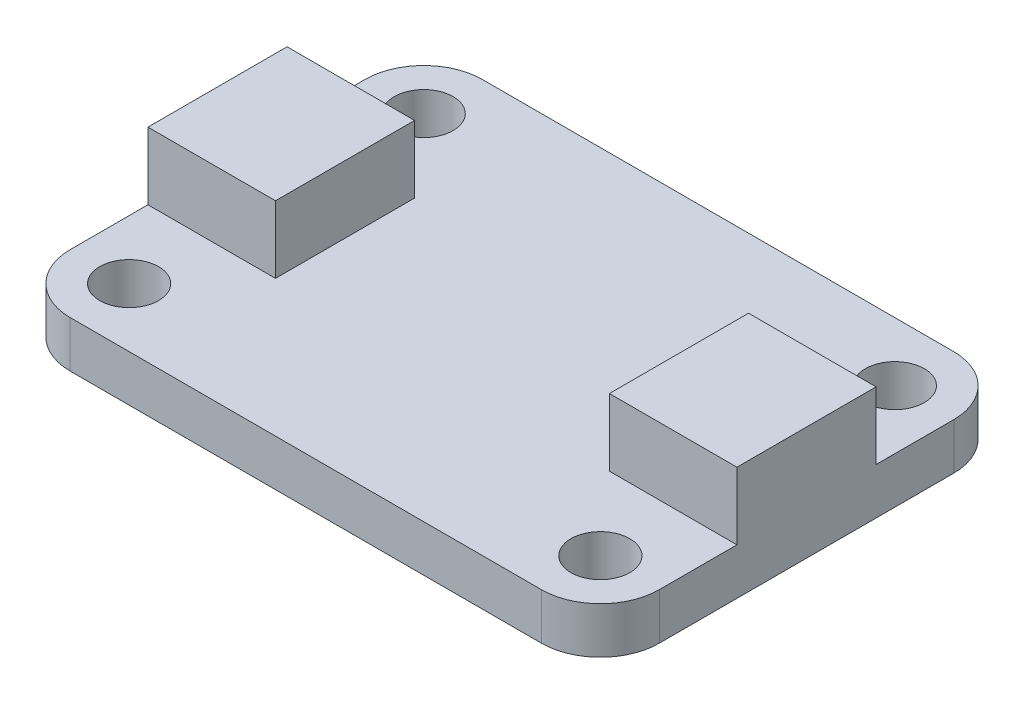
SolidWorks part; units mm, degrees
ref_plane "Front Plane" through (0, 0, 0) normal (0, 0, 1) x (1, 0, 0)
ref_plane "Top Plane" through (0, 0, 0) normal (0, 1, 0) x (1, 0, 0)
ref_plane "Right Plane" through (0, 0, 0) normal (1, 0, 0) x (0, 0, -1)
sketch "Sketch1" plane through (0, 0, 0) normal (0, 1, 0) x (1, 0, 0)
  line L1 (0, 0) -> (25.4, 0)
  line L2 (0, 0) -> (0, 17.78)
  line L3 (0, 17.78) -> (25.4, 17.78)
  line L4 (25.4, 0) -> (25.4, 17.78)
  dimension "D1" = 25.4
  dimension "D2" = 17.78
extrude "Boss-Extrude1" add sketch "Sketch1" along normal blind 2
sketch "Sketch2" plane through (0, 2, 0) normal (0, 1, 0) x (1, 0, 0)
  line L0 (0, 8.89) -> (25.4, 8.89) construction
  line L1 (0, 17.78) -> (0, 0) construction
  line L2 (25.4, 0) -> (25.4, 17.78) construction
  line L3 (12.7, 17.78) -> (12.7, 0) construction
  line L4 (25.4, 17.78) -> (0, 17.78) construction
  line L5 (0, 0) -> (25.4, 0) construction
  circle A0 centre (2.54, 15.24) radius 1.27
  circle A1 centre (22.86, 15.24) radius 1.27
  circle A2 centre (22.86, 2.54) radius 1.27
  circle A3 centre (2.54, 2.54) radius 1.27
  point P14 (0, 0)
  point P15 (22.86, 15.24)
  point P16 (1.2788, 17.148)
  point P21 (22.86, 2.54)
  dimension "D1" = 2.54
  dimension "D2" = 2.54
  dimension "D3" = 2.54
extrude "Cut-Extrude1" cut sketch "Sketch2" against normal through all
sketch "Sketch3" plane through (0, 2, 0) normal (0, 1, 0) x (1, 0, 0)
  line L0 (0, 8.89) -> (25.4, 8.89) construction
  line L1 (0, 17.78) -> (0, 0) construction
  line L2 (25.4, 0) -> (25.4, 17.78) construction
  line L3 (12.7, 17.78) -> (12.7, 0) construction
  line L4 (25.4, 17.78) -> (0, 17.78) construction
  line L5 (0, 0) -> (25.4, 0) construction
  line L6 (25.4, 5.89) -> (19.9, 5.89)
  line L7 (0, 11.89) -> (5.5, 11.89)
  line L8 (0, 11.89) -> (0, 5.89)
  line L9 (0, 5.89) -> (5.5, 5.89)
  line L10 (5.5, 11.89) -> (5.5, 5.89)
  line L11 (19.9, 11.89) -> (19.9, 5.89)
  line L12 (25.4, 11.89) -> (19.9, 11.89)
  line L13 (25.4, 11.89) -> (25.4, 5.89)
  point P16 (0, 0)
  point P17 (0, 0)
  point P18 (0, 8.89)
  dimension "D1" = 6
  dimension "D2" = 5.5
extrude "Boss-Extrude2" add sketch "Sketch3" along normal blind 2.9
fillet "Fillet1" radius 2.54 4 edges at (25.4, 1, -17.78) (25.4, 1, 0) (0, 1, 0) (0, 1, -17.78)
